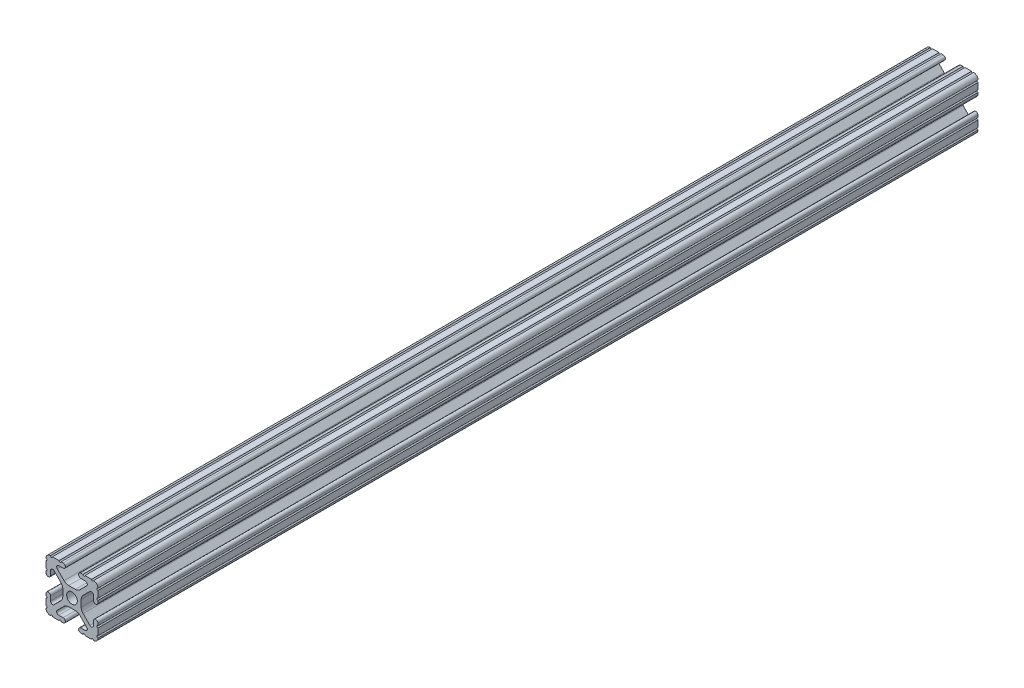
SolidWorks part; units mm, degrees
material "6061-T6 (SS)"
ref_plane "Front Plane" through (0, 0, 0) normal (0, 0, 1) x (1, 0, 0)
ref_plane "Top Plane" through (0, 0, 0) normal (0, 1, 0) x (1, 0, 0)
ref_plane "Right Plane" through (0, 0, 0) normal (1, 0, 0) x (0, 0, -1)
ref_plane "Plane1" through (0, 0, -450.85) normal (0, 0, -1) x (-1, 0, 0)
sketch "Sketch1" plane through (0, 0, -450.85) normal (0, 0, -1) x (-1, 0, 0)
  line L0 (12.7, -9.5504) -> (12.7, -6.3331)
  line L1 (12.7, -5.3171) -> (12.7, -4.3434)
  line L2 (10.4902, -4.3434) -> (10.4902, -6.4748)
  line L3 (8.7558, -7.1932) -> (5.4257, -3.8632)
  line L4 (4.4958, -1.6181) -> (4.4958, 1.6181)
  line L5 (5.4257, 3.8632) -> (8.7558, 7.1932)
  line L6 (10.4902, 6.4748) -> (10.4902, 4.3434)
  line L7 (12.7, 4.3434) -> (12.7, 5.3171)
  line L8 (12.7, 6.3331) -> (12.7, 9.5504)
  line L9 (9.5504, 12.7) -> (6.3331, 12.7)
  line L10 (5.3171, 12.7) -> (4.3434, 12.7)
  line L11 (4.3434, 10.4902) -> (6.4748, 10.4902)
  line L12 (7.1932, 8.7558) -> (3.8632, 5.4257)
  line L13 (1.6181, 4.4958) -> (-1.6181, 4.4958)
  line L14 (-3.8632, 5.4257) -> (-7.1932, 8.7558)
  line L15 (-6.4748, 10.4902) -> (-4.3434, 10.4902)
  line L16 (-4.3434, 12.7) -> (-5.3171, 12.7)
  line L17 (-6.3331, 12.7) -> (-9.5504, 12.7)
  line L18 (-12.7, 9.5504) -> (-12.7, 6.3331)
  line L19 (-12.7, 5.3171) -> (-12.7, 4.3434)
  line L20 (-10.4902, 4.3434) -> (-10.4902, 6.4748)
  line L21 (-8.7558, 7.1932) -> (-5.4257, 3.8632)
  line L22 (-4.4958, 1.6181) -> (-4.4958, -1.6181)
  line L23 (-5.4257, -3.8632) -> (-8.7558, -7.1932)
  line L24 (-10.4902, -6.4748) -> (-10.4902, -4.3434)
  line L25 (-12.7, -4.3434) -> (-12.7, -5.3171)
  line L26 (-12.7, -6.3331) -> (-12.7, -9.5504)
  line L27 (-9.5504, -12.7) -> (-6.3331, -12.7)
  line L28 (-5.3171, -12.7) -> (-4.3434, -12.7)
  line L29 (-4.3434, -10.4902) -> (-6.4748, -10.4902)
  line L30 (-7.1932, -8.7558) -> (-3.8632, -5.4257)
  line L31 (-1.6181, -4.4958) -> (1.6181, -4.4958)
  line L32 (3.8632, -5.4257) -> (7.1932, -8.7558)
  line L33 (6.4748, -10.4902) -> (4.3434, -10.4902)
  line L34 (4.3434, -12.7) -> (5.3171, -12.7)
  line L35 (6.3331, -12.7) -> (9.5504, -12.7)
  arc A0 (12.6998, -10.5664) -> (12.7, -9.5504) centre (12.7, -10.0584) cw
  arc A1 (12.7, -6.3331) -> (12.7, -5.3171) centre (12.7, -5.8251) cw
  arc A2 (12.7, -4.3434) -> (10.4902, -4.3434) centre (11.5951, -4.3434) ccw
  arc A3 (10.4902, -6.4748) -> (8.7558, -7.1932) centre (9.4742, -6.4748) cw
  arc A4 (5.4257, -3.8632) -> (4.4958, -1.6181) centre (7.6708, -1.6181) cw
  arc A5 (4.4958, 1.6181) -> (5.4257, 3.8632) centre (7.6708, 1.6181) cw
  arc A6 (8.7558, 7.1932) -> (10.4902, 6.4748) centre (9.4742, 6.4748) cw
  arc A7 (10.4902, 4.3434) -> (12.7, 4.3434) centre (11.5951, 4.3434) ccw
  arc A8 (12.7, 5.3171) -> (12.7, 6.3331) centre (12.7, 5.8251) cw
  arc A9 (12.7, 9.5504) -> (12.6998, 10.5664) centre (12.7, 10.0584) cw
  arc A10 (12.6998, 10.5664) -> (10.5664, 12.6998) centre (10.5918, 10.5918) ccw
  arc A11 (10.5664, 12.6998) -> (9.5504, 12.7) centre (10.0584, 12.7) cw
  arc A12 (6.3331, 12.7) -> (5.3171, 12.7) centre (5.8251, 12.7) cw
  arc A13 (4.3434, 12.7) -> (4.3434, 10.4902) centre (4.3434, 11.5951) ccw
  arc A14 (6.4748, 10.4902) -> (7.1932, 8.7558) centre (6.4748, 9.4742) cw
  arc A15 (3.8632, 5.4257) -> (1.6181, 4.4958) centre (1.6181, 7.6708) cw
  arc A16 (-1.6181, 4.4958) -> (-3.8632, 5.4257) centre (-1.6181, 7.6708) cw
  arc A17 (-7.1932, 8.7558) -> (-6.4748, 10.4902) centre (-6.4748, 9.4742) cw
  arc A18 (-4.3434, 10.4902) -> (-4.3434, 12.7) centre (-4.3434, 11.5951) ccw
  arc A19 (-5.3171, 12.7) -> (-6.3331, 12.7) centre (-5.8251, 12.7) cw
  arc A20 (-9.5504, 12.7) -> (-10.5664, 12.6998) centre (-10.0584, 12.7) cw
  arc A21 (-10.5664, 12.6998) -> (-12.6998, 10.5664) centre (-10.5918, 10.5918) ccw
  arc A22 (-12.6998, 10.5664) -> (-12.7, 9.5504) centre (-12.7, 10.0584) cw
  arc A23 (-12.7, 6.3331) -> (-12.7, 5.3171) centre (-12.7, 5.8251) cw
  arc A24 (-12.7, 4.3434) -> (-10.4902, 4.3434) centre (-11.5951, 4.3434) ccw
  arc A25 (-10.4902, 6.4748) -> (-8.7558, 7.1932) centre (-9.4742, 6.4748) cw
  arc A26 (-5.4257, 3.8632) -> (-4.4958, 1.6181) centre (-7.6708, 1.6181) cw
  arc A27 (-4.4958, -1.6181) -> (-5.4257, -3.8632) centre (-7.6708, -1.6181) cw
  arc A28 (-8.7558, -7.1932) -> (-10.4902, -6.4748) centre (-9.4742, -6.4748) cw
  arc A29 (-10.4902, -4.3434) -> (-12.7, -4.3434) centre (-11.5951, -4.3434) ccw
  arc A30 (-12.7, -5.3171) -> (-12.7, -6.3331) centre (-12.7, -5.8251) cw
  arc A31 (-12.7, -9.5504) -> (-12.6998, -10.5664) centre (-12.7, -10.0584) cw
  arc A32 (-12.6998, -10.5664) -> (-10.5664, -12.6998) centre (-10.5918, -10.5918) ccw
  arc A33 (-10.5664, -12.6998) -> (-9.5504, -12.7) centre (-10.0584, -12.7) cw
  arc A34 (-6.3331, -12.7) -> (-5.3171, -12.7) centre (-5.8251, -12.7) cw
  arc A35 (-4.3434, -12.7) -> (-4.3434, -10.4902) centre (-4.3434, -11.5951) ccw
  arc A36 (-6.4748, -10.4902) -> (-7.1932, -8.7558) centre (-6.4748, -9.4742) cw
  arc A37 (-3.8632, -5.4257) -> (-1.6181, -4.4958) centre (-1.6181, -7.6708) cw
  arc A38 (1.6181, -4.4958) -> (3.8632, -5.4257) centre (1.6181, -7.6708) cw
  arc A39 (7.1932, -8.7558) -> (6.4748, -10.4902) centre (6.4748, -9.4742) cw
  arc A40 (4.3434, -10.4902) -> (4.3434, -12.7) centre (4.3434, -11.5951) ccw
  arc A41 (5.3171, -12.7) -> (6.3331, -12.7) centre (5.8251, -12.7) cw
  arc A42 (9.5504, -12.7) -> (10.5664, -12.6998) centre (10.0584, -12.7) cw
  arc A43 (10.5664, -12.6998) -> (12.6998, -10.5664) centre (10.5918, -10.5918) ccw
  circle A44 centre (0, 0) radius 2.6035
extrude "Boss-Extrude1" add sketch "Sketch1" against normal mid plane 430.2125
